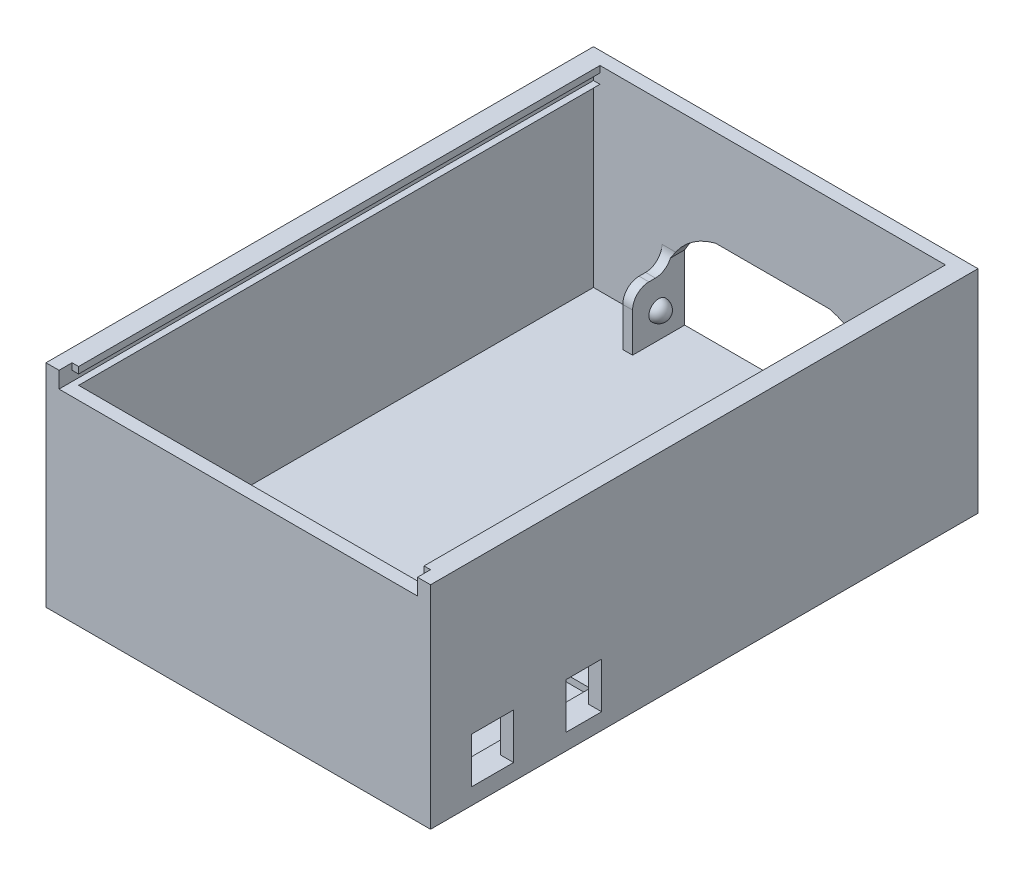
SolidWorks part; units mm, degrees
ref_plane "Front Plane" through (0, 0, 0) normal (0, 0, 1) x (1, 0, 0)
ref_plane "Top Plane" through (0, 0, 0) normal (0, 1, 0) x (1, 0, 0)
ref_plane "Right Plane" through (0, 0, 0) normal (1, 0, 0) x (0, 0, -1)
sketch "Sketch1" plane through (0, 0, 0) normal (0, 1, 0) x (1, 0, 0)
  line L1 (0, 0) -> (118, 0)
  line L2 (0, 0) -> (0, 168)
  line L3 (0, 168) -> (118, 168)
  line L4 (118, 0) -> (118, 168)
extrude "Boss-Extrude1" add sketch "Sketch1" along normal blind 5
sketch "Sketch2" plane through (0, 5, 0) normal (0, 1, 0) x (1, 0, 0)
  line L0 (0, 0) -> (4, 0) construction
  line L1 (0, 0) -> (118, 0) construction
  line L3 (118, 168) -> (114, 168) construction
  line L4 (118, 168) -> (0, 168) construction
  line L7 (4, 4) -> (114, 4)
  line L8 (4, 4) -> (4, 164)
  line L9 (4, 164) -> (114, 164)
  line L10 (114, 4) -> (114, 164)
  line L11 (0, 0) -> (118, 0)
  line L12 (0, 0) -> (0, 168)
  line L13 (0, 168) -> (118, 168)
  line L14 (118, 0) -> (118, 168)
  dimension "D1" = 4
  dimension "D2" = 4
  dimension "D3" = 4
  dimension "D4" = 4
extrude "Boss-Extrude2" add sketch "Sketch2" along normal blind 60
sketch "Sketch3" plane through (114, 0, 0) normal (-1, 0, 0) x (0, 0, 1)
  line L0 (-4, 5) -> (-12.5, 5) construction
  line L1 (-4, 5) -> (-164, 5) construction
  line L2 (-12.5, 5) -> (-12.5, 19)
  line L3 (-12.5, 19) -> (-25.5, 19)
  line L4 (-25.5, 19) -> (-25.5, 5)
  line L5 (-25.5, 5) -> (-12.5, 5)
  line L6 (-4, 65) -> (-4, 5) construction
  line L8 (-41.5, 5) -> (-41.5, 19)
  line L9 (-41.5, 19) -> (-52.5, 19)
  line L10 (-52.5, 19) -> (-52.5, 5)
  line L11 (-52.5, 5) -> (-41.5, 5)
  dimension "D1" = 8.5
  dimension "D2" = 14
  dimension "D3" = 13
  dimension "D4" = 11
  dimension "D5" = 16
  dimension "D6" = 14
extrude "Cut-Extrude1" cut sketch "Sketch3" against normal blind 10
sketch "Sketch4" plane through (0, 5, 0) normal (0, 1, 0) x (1, 0, 0)
  line L0 (114, 4) -> (110, 4) construction
  line L1 (4, 4) -> (114, 4) construction
  line L2 (110, 4) -> (110, 5) construction
  line L7 (114, 25.5) -> (114, 41.5) construction
  line L8 (110, 5) -> (110, 6.5) construction
  line L9 (110, 57) -> (12, 57)
  line L10 (12, 57) -> (12, 6.5)
  line L11 (12, 6.5) -> (110, 6.5)
  line L12 (110, 6.5) -> (110, 57)
  dimension "D1" = 2.5
  dimension "D2" = 4
  dimension "D3" = 98
  dimension "D4" = 50.5
extrude "Cut-Extrude2" cut sketch "Sketch4" against normal blind 2
sketch "Sketch5" plane through (0, 0, -164) normal (0, 0, 1) x (1, 0, 0)
  line L0 (59, 5) -> (90, 5)
  line L1 (114, 5) -> (4, 5) construction
  line L2 (59, 5) -> (28, 5)
  line L3 (28, 5) -> (28, 25)
  line L5 (90, 25) -> (90, 5)
  line L7 (41.5, 35.5) -> (76.5, 35.5)
  arc A0 (28, 25) -> (41.5, 35.5) centre (46.5058, 15.1354) cw
  arc A1 (90, 25) -> (76.5, 35.5) centre (71.4942, 15.1354) ccw
  dimension "D1" = 62
  dimension "D2" = 30.5
extrude "Cut-Extrude3" cut sketch "Sketch5" against normal blind 10
sketch "Sketch6" plane through (0, 0, -164) normal (0, 0, 1) x (1, 0, 0)
  line L0 (28, 5) -> (28, 22)
  line L2 (28, 25) -> (28, 5) construction
  line L3 (28, 22) -> (25, 22)
  line L4 (25, 22) -> (25, 5)
  line L5 (28, 5) -> (4, 5) construction
  line L6 (25, 5) -> (28, 5)
  line L7 (59, 35.5) -> (59, 5) construction
  line L8 (76.5, 35.5) -> (41.5, 35.5) construction
  line L9 (93, 22) -> (93, 5)
  line L10 (90, 22) -> (93, 22)
  line L11 (90, 5) -> (90, 22)
  line L12 (93, 5) -> (90, 5)
extrude "Boss-Extrude3" add sketch "Sketch6" along normal blind 12
sketch "Sketch7" plane through (28, 0, 0) normal (1, 0, 0) x (0, 0, -1)
  line L0 (168, 5) -> (152, 5) construction
  line L3 (157, 13) -> (163, 13)
  line L4 (152, 5) -> (152, 22) construction
  arc A0 (157, 13) -> (163, 13) centre (160, 13) ccw
  point P5 (152, 15.6516)
  dimension "D1" = 8
  dimension "D3" = 3
  dimension "D2" = 8
revolve "Revolve1" add sketch "Sketch7" angle 360 about L3
sketch "Sketch9" plane through (90, 0, 0) normal (-1, 0, 0) x (0, 0, 1)
  line L3 (-163, 13) -> (-157, 13)
  arc A0 (-163, 13) -> (-157, 13) centre (-160, 13) ccw
revolve "Revolve2" add sketch "Sketch9" angle 180 about L3
fillet "Fillet1" radius 5 4 edges at (91.5, 22, -152) (91.5, 22, -164) (26.5, 22, -164) (26.5, 22, -152)
sketch "Sketch10" plane through (0, 0, -4) normal (0, 0, -1) x (-1, 0, 0)
  line L0 (-4, 65) -> (-4, 60)
  line L1 (-4, 65) -> (-4, 5) construction
  line L2 (-4, 60) -> (-114, 60)
  line L3 (-114, 65) -> (-114, 5) construction
  line L4 (-114, 60) -> (-114, 65)
  line L5 (-114, 65) -> (-4, 65)
extrude "Cut-Extrude4" cut sketch "Sketch10" against normal blind 12
sketch "Sketch11" plane through (0, 0, -4) normal (0, 0, -1) x (-1, 0, 0)
  line L0 (-114, 60) -> (-114, 58)
  line L1 (-114, 60) -> (-114, 5) construction
  line L2 (-114, 58) -> (-112, 60)
  line L3 (-114, 60) -> (-4, 60) construction
  line L4 (-114, 60) -> (-112, 60)
  line L5 (-59, 60) -> (-59, 43.9753) construction
  line L6 (-4, 60) -> (-4, 58)
  line L7 (-4, 58) -> (-6, 60)
  line L8 (-4, 60) -> (-6, 60)
  line L9 (-114, 60) -> (-114, 63) construction
  line L10 (-114, 63) -> (-112, 63)
  line L11 (-114, 63) -> (-114, 65)
  line L12 (-114, 65) -> (-112, 65)
  line L13 (-112, 65) -> (-112, 63)
  line L14 (-4, 65) -> (-6, 65)
  line L15 (-4, 63) -> (-4, 65)
  line L16 (-4, 63) -> (-6, 63)
  line L17 (-6, 65) -> (-6, 63)
  dimension "D1" = 45
extrude "Boss-Extrude4" add sketch "Sketch11" along normal up to surface (160 mm away) up to face at (59, 27.6052, -164)
